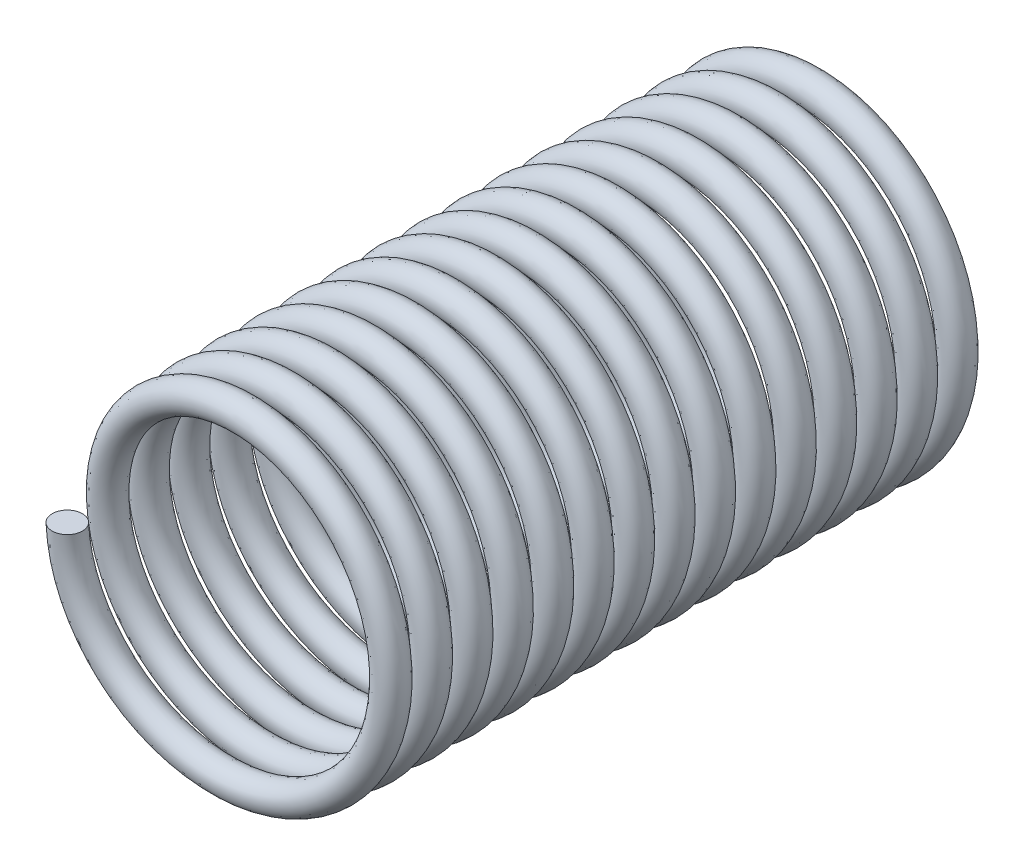
SolidWorks part; units mm, degrees
ref_plane "Front Plane" through (0, 0, 0) normal (0, 0, 1) x (1, 0, 0)
ref_plane "Top Plane" through (0, 0, 0) normal (0, 1, 0) x (1, 0, 0)
ref_plane "Right Plane" through (0, 0, 0) normal (1, 0, 0) x (0, 0, -1)
sketch "Sketch1" plane through (0, 0, 0) normal (0, 0, 1) x (1, 0, 0)
  circle A0 centre (0, 0) radius 5
  point P3 (0, 0)
curve "Helix/Spiral1" pitch 1.3333 height 20 turns 15
sketch "Sketch2" plane through (0, 0, 0) normal (0, 1, 0) x (1, 0, 0)
  circle A1 centre (-5, -20) radius 0.4971
  spline S1 degree 3 poles (-5, 0) (-5, -0.0276) (-4.7397, -0.0834) (-3.6276, -0.1666) (-1.9632, -0.25) (0, -0.3333) (1.9632, -0.4167) (3.6276, -0.5) (4.7397, -0.5833) (5.1302, -0.6667) (4.7397, -0.75) (3.6276, -0.8333) (1.4084, -0.9444) (-1.4084, -1.0556) (-3.6276, -1.1667) (-4.7397, -1.25) (-5.1302, -1.3333) (-4.7397, -1.4167) (-3.6276, -1.5) (-1.4084, -1.6111) (1.4084, -1.7222) (3.6276, -1.8333) (4.7397, -1.9167) (5.1302, -2) (4.7397, -2.0833) (3.6276, -2.1667) (1.4084, -2.2778) (-1.4084, -2.3889) (-3.6276, -2.5) (-4.7397, -2.5833) (-5.1302, -2.6667) (-4.7397, -2.75) (-3.6276, -2.8333) (-1.4084, -2.9444) (1.4084, -3.0556) (3.6276, -3.1667) (4.7397, -3.25) (5.1302, -3.3333) (4.7397, -3.4167) (3.6276, -3.5) (1.4084, -3.6111) (-1.4084, -3.7222) (-3.6276, -3.8333) (-4.7397, -3.9167) (-5.1302, -4) (-4.7397, -4.0833) (-3.6276, -4.1667) (-1.4084, -4.2778) (1.4084, -4.3889) (3.6276, -4.5) (4.7397, -4.5833) (5.1302, -4.6667) (4.7397, -4.75) (3.6276, -4.8333) (1.4084, -4.9444) (-1.4084, -5.0556) (-3.6276, -5.1667) (-4.7397, -5.25) (-5.1302, -5.3333) (-4.7397, -5.4167) (-3.6276, -5.5) (-1.4084, -5.6111) (1.4084, -5.7222) (3.6276, -5.8333) (4.7397, -5.9167) (5.1302, -6) (4.7397, -6.0833) (3.6276, -6.1667) (1.4084, -6.2778) (-1.4084, -6.3889) (-3.6276, -6.5) (-4.7397, -6.5833) (-5.1302, -6.6667) (-4.7397, -6.75) (-3.6276, -6.8333) (-1.4084, -6.9444) (1.4084, -7.0556) (3.6276, -7.1667) (4.7397, -7.25) (5.1302, -7.3333) (4.7397, -7.4167) (3.6276, -7.5) (1.4084, -7.6111) (-1.4084, -7.7222) (-3.6276, -7.8333) (-4.7397, -7.9167) (-5.1302, -8) (-4.7397, -8.0833) (-3.6276, -8.1667) (-1.4084, -8.2778) (1.4084, -8.3889) (3.6276, -8.5) (4.7397, -8.5833) (5.1302, -8.6667) (4.7397, -8.75) (3.6276, -8.8333) (1.4084, -8.9444) (-1.4084, -9.0556) (-3.6276, -9.1667) (-4.7397, -9.25) (-5.1302, -9.3333) (-4.7397, -9.4167) (-3.6276, -9.5) (-1.4084, -9.6111) (1.4084, -9.7222) (3.6276, -9.8333) (4.7397, -9.9167) (5.1302, -10) (4.7397, -10.0833) (3.6276, -10.1667) (1.4084, -10.2778) (-1.4084, -10.3889) (-3.6276, -10.5) (-4.7397, -10.5833) (-5.1302, -10.6667) (-4.7397, -10.75) (-3.6276, -10.8333) (-1.4084, -10.9444) (1.4084, -11.0556) (3.6276, -11.1667) (4.7397, -11.25) (5.1302, -11.3333) (4.7397, -11.4167) (3.6276, -11.5) (1.4084, -11.6111) (-1.4084, -11.7222) (-3.6276, -11.8333) (-4.7397, -11.9167) (-5.1302, -12) (-4.7397, -12.0833) (-3.6276, -12.1667) (-1.4084, -12.2778) (1.4084, -12.3889) (3.6276, -12.5) (4.7397, -12.5833) (5.1302, -12.6667) (4.7397, -12.75) (3.6276, -12.8333) (1.4084, -12.9444) (-1.4084, -13.0556) (-3.6276, -13.1667) (-4.7397, -13.25) (-5.1302, -13.3333) (-4.7397, -13.4167) (-3.6276, -13.5) (-1.4084, -13.6111) (1.4084, -13.7222) (3.6276, -13.8333) (4.7397, -13.9167) (5.1302, -14) (4.7397, -14.0833) (3.6276, -14.1667) (1.4084, -14.2778) (-1.4084, -14.3889) (-3.6276, -14.5) (-4.7397, -14.5833) (-5.1302, -14.6667) (-4.7397, -14.75) (-3.6276, -14.8333) (-1.4084, -14.9444) (1.4084, -15.0556) (3.6276, -15.1667) (4.7397, -15.25) (5.1302, -15.3333) (4.7397, -15.4167) (3.6276, -15.5) (1.4084, -15.6111) (-1.4084, -15.7222) (-3.6276, -15.8333) (-4.7397, -15.9167) (-5.1302, -16) (-4.7397, -16.0833) (-3.6276, -16.1667) (-1.4084, -16.2778) (1.4084, -16.3889) (3.6276, -16.5) (4.7397, -16.5833) (5.1302, -16.6667) (4.7397, -16.75) (3.6276, -16.8333) (1.4084, -16.9444) (-1.4084, -17.0556) (-3.6276, -17.1667) (-4.7397, -17.25) (-5.1302, -17.3333) (-4.7397, -17.4167) (-3.6276, -17.5) (-1.4084, -17.6111) (1.4084, -17.7222) (3.6276, -17.8333) (4.7397, -17.9167) (5.1302, -18) (4.7397, -18.0833) (3.6276, -18.1667) (1.4084, -18.2778) (-1.4084, -18.3889) (-3.6276, -18.5) (-4.7397, -18.5833) (-5.1302, -18.6667) (-4.7397, -18.75) (-3.6276, -18.8333) (-1.4084, -18.9444) (1.4084, -19.0556) (3.6276, -19.1667) (4.7397, -19.25) (5.1302, -19.3333) (4.7397, -19.4167) (3.6276, -19.5) (1.9632, -19.5833) (0, -19.6667) (-1.9632, -19.75) (-3.6276, -19.8334) (-4.7397, -19.9166) (-5, -19.9724) (-5, -20) knots 0 0 0 0 0.004167 0.008333 0.0125 0.016667 0.020833 0.025 0.029167 0.033333 0.0375 0.041667 0.045833 0.054167 0.058333 0.0625 0.066667 0.070833 0.075 0.079167 0.0875 0.091667 0.095833 0.1 0.104167 0.108333 0.1125 0.120833 0.125 0.129167 0.133333 0.1375 0.141667 0.145833 0.154167 0.158333 0.1625 0.166667 0.170833 0.175 0.179167 0.1875 0.191667 0.195833 0.2 0.204167 0.208333 0.2125 0.220833 0.225 0.229167 0.233333 0.2375 0.241667 0.245833 0.254167 0.258333 0.2625 0.266667 0.270833 0.275 0.279167 0.2875 0.291667 0.295833 0.3 0.304167 0.308333 0.3125 0.320833 0.325 0.329167 0.333333 0.3375 0.341667 0.345833 0.354167 0.358333 0.3625 0.366667 0.370833 0.375 0.379167 0.3875 0.391667 0.395833 0.4 0.404167 0.408333 0.4125 0.420833 0.425 0.429167 0.433333 0.4375 0.441667 0.445833 0.454167 0.458333 0.4625 0.466667 0.470833 0.475 0.479167 0.4875 0.491667 0.495833 0.5 0.504167 0.508333 0.5125 0.520833 0.525 0.529167 0.533333 0.5375 0.541667 0.545833 0.554167 0.558333 0.5625 0.566667 0.570833 0.575 0.579167 0.5875 0.591667 0.595833 0.6 0.604167 0.608333 0.6125 0.620833 0.625 0.629167 0.633333 0.6375 0.641667 0.645833 0.654167 0.658333 0.6625 0.666667 0.670833 0.675 0.679167 0.6875 0.691667 0.695833 0.7 0.704167 0.708333 0.7125 0.720833 0.725 0.729167 0.733333 0.7375 0.741667 0.745833 0.754167 0.758333 0.7625 0.766667 0.770833 0.775 0.779167 0.7875 0.791667 0.795833 0.8 0.804167 0.808333 0.8125 0.820833 0.825 0.829167 0.833333 0.8375 0.841667 0.845833 0.854167 0.858333 0.8625 0.866667 0.870833 0.875 0.879167 0.8875 0.891667 0.895833 0.9 0.904167 0.908333 0.9125 0.920833 0.925 0.929167 0.933333 0.9375 0.941667 0.945833 0.954167 0.958333 0.9625 0.966667 0.970833 0.975 0.979167 0.983333 0.9875 0.991667 0.995833 1 1 1 1 construction
sweep "Sweep1" add profiles "Sketch2" path "Helix/Spiral1"
sketch "Sketch3" plane through (0, 0, 0) normal (0, 1, 0) x (1, 0, 0)
  line L0 (0, -21.5886) -> (0, 2.8962) construction
